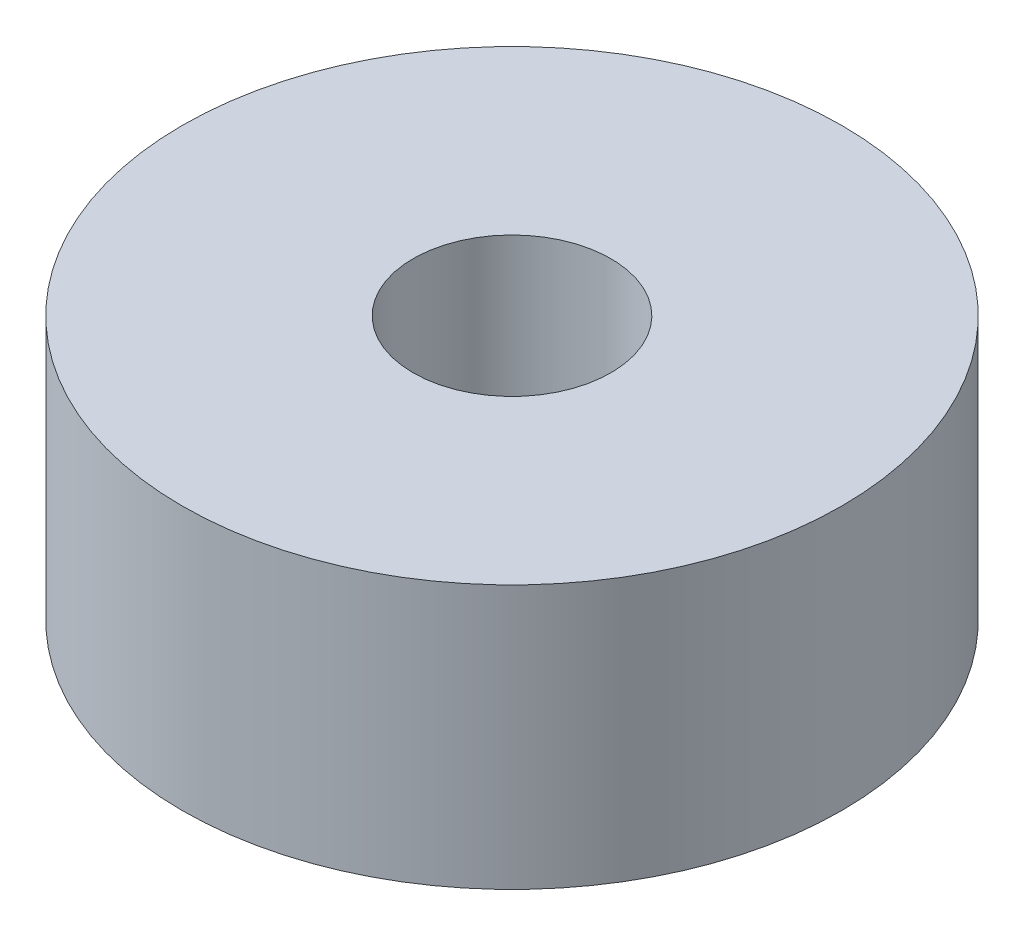
SolidWorks part; units mm, degrees
ref_plane "Front Plane" through (0, 0, 0) normal (0, 0, 1) x (1, 0, 0)
ref_plane "Top Plane" through (0, 0, 0) normal (0, 1, 0) x (1, 0, 0)
ref_plane "Right Plane" through (0, 0, 0) normal (1, 0, 0) x (0, 0, -1)
sketch "Sketch1" plane through (0, 0, 0) normal (0, 1, 0) x (1, 0, 0)
  circle A0 centre (0, 0) radius 5
  circle A1 centre (0, 0) radius 1.5
extrude "Boss-Extrude1" add sketch "Sketch1" along normal blind 4 contours A0 A1
